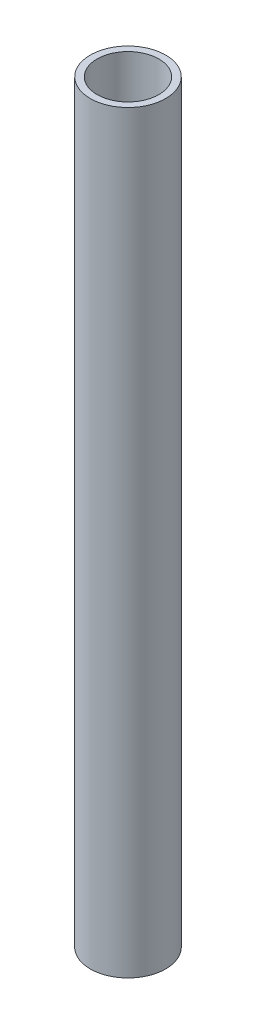
SolidWorks part; units mm, degrees
ref_plane "Front Plane" through (0, 0, 0) normal (0, 0, 1) x (1, 0, 0)
ref_plane "Top Plane" through (0, 0, 0) normal (0, 1, 0) x (1, 0, 0)
ref_plane "Right Plane" through (0, 0, 0) normal (1, 0, 0) x (0, 0, -1)
sketch "Sketch1" plane through (0, 0, 0) normal (0, 1, 0) x (1, 0, 0)
  circle A0 centre (0, 0) radius 12.7
  circle A1 centre (0, 0) radius 10.414
  dimension "D1" = 25.4
  dimension "D2" = 20.828
extrude "Boss-Extrude1" add sketch "Sketch1" along normal blind 254
